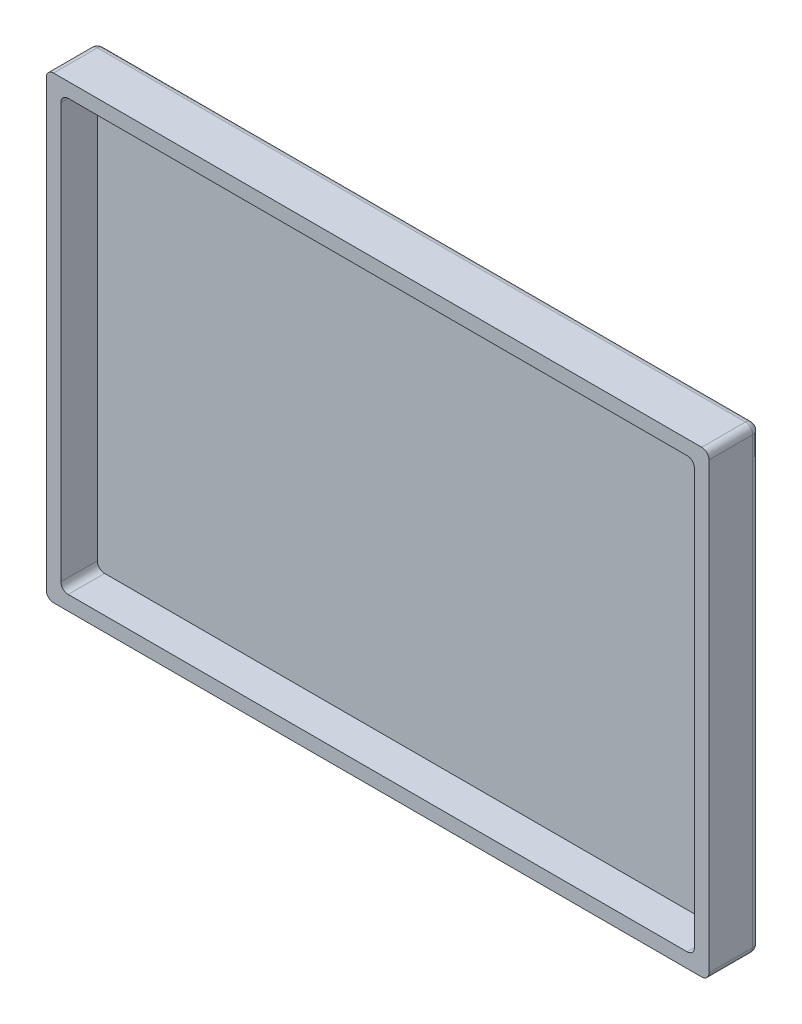
SolidWorks part; units mm, degrees
ref_plane "Plano frontal" through (0, 0, 0) normal (0, 0, 1) x (1, 0, 0)
ref_plane "Plano superior" through (0, 0, 0) normal (0, 1, 0) x (1, 0, 0)
ref_plane "Plano direito" through (0, 0, 0) normal (1, 0, 0) x (0, 0, -1)
sketch "Esboço1" plane through (0, 0, 0) normal (0, 0, 1) x (1, 0, 0)
  line L1 (-44.7633, 14.2986) -> (42.2367, 14.2986)
  line L2 (-44.7633, 14.2986) -> (-44.7633, -44.7014)
  line L3 (-44.7633, -44.7014) -> (42.2367, -44.7014)
  line L4 (42.2367, 14.2986) -> (42.2367, -44.7014)
  line L5 (-46.7633, 16.2986) -> (44.2367, 16.2986)
  line L6 (-46.7633, 16.2986) -> (-46.7633, -46.7014)
  line L7 (-46.7633, -46.7014) -> (44.2367, -46.7014)
  line L8 (44.2367, 16.2986) -> (44.2367, -46.7014)
  dimension "D1" = 59
  dimension "D2" = 87
  dimension "D3" = 2
  dimension "D4" = 2
  dimension "D5" = 2
  dimension "D6" = 2
extrude "Ressalto-extrusão1" add sketch "Esboço1" along normal blind 5
sketch "Esboço2" plane through (0, 0, 0) normal (0, 0, -1) x (-1, 0, 0)
  line L1 (-44.2367, 16.2986) -> (46.7633, 16.2986)
  line L2 (-44.2367, 16.2986) -> (-44.2367, -46.7014)
  line L3 (-44.2367, -46.7014) -> (46.7633, -46.7014)
  line L4 (46.7633, 16.2986) -> (46.7633, -46.7014)
extrude "Ressalto-extrusão2" add sketch "Esboço2" along normal blind 2
fillet "Filete6" radius 1 1 edges at (42.2367, 14.2986, 2.5)
fillet "Filete7" radius 1 3 edges at (-44.7633, 14.2986, 2.5) (-44.7633, -44.7014, 2.5) (42.2367, -44.7014, 2.5)
fillet "Filete10" radius 1 1 edges at (-46.7633, -46.7014, 1.5)
fillet "Filete11" radius 1 3 edges at (44.2367, -46.7014, 1.5) (44.2367, 16.2986, 1.5) (-46.7633, 16.2986, 1.5)
fillet "Filete12" radius 1 8 edges at (-46.4704, 16.0057, -2) (-46.4704, -46.4085, -2) (43.9438, -46.4085, -2) (43.9438, 16.0057, -2) (-46.7633, -15.2014, -2) (-1.2633, -46.7014, -2) (44.2367, -15.2014, -2) (-1.2633, 16.2986, -2)
